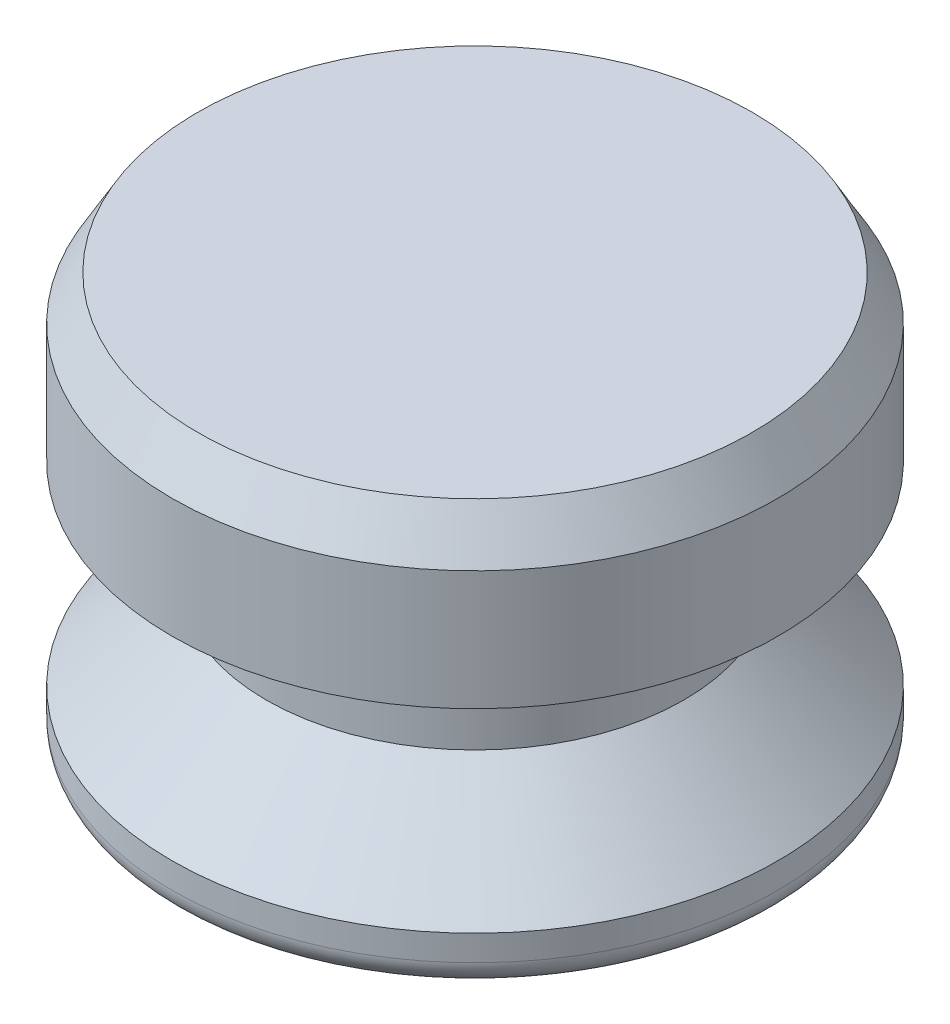
SolidWorks part; units mm, degrees
ref_plane "Front Plane" through (0, 0, 0) normal (0, 0, 1) x (1, 0, 0)
ref_plane "Top Plane" through (0, 0, 0) normal (0, 1, 0) x (1, 0, 0)
ref_plane "Right Plane" through (0, 0, 0) normal (1, 0, 0) x (0, 0, -1)
sketch "Sketch1" plane through (0, 0, 0) normal (0, 0, 1) x (1, 0, 0)
  line L0 (0, 0) -> (0, 12.7) construction
  line L1 (0, 0) -> (-9.398, 0)
  line L2 (-9.398, 0) -> (-9.398, 1.5875)
  line L4 (-6.477, 4.445) -> (-6.477, 7.62)
  line L5 (-6.477, 7.62) -> (-9.398, 7.62)
  line L6 (-9.398, 7.62) -> (-9.398, 12.7)
  line L7 (-9.398, 12.7) -> (0, 12.7)
  line L8 (-9.525, 16.6801) -> (-9.525, -9.6051) construction
  line L9 (0, 0) -> (0, 12.7)
  line L10 (-6.477, 4.445) -> (-9.398, 1.5875)
  dimension "D1" = 12.7
  dimension "D2" = 9.398
  dimension "D3" = 3.175
  dimension "D4" = 1.5875
  dimension "D5" = 9.525
  dimension "D6" = 6.477
  dimension "D7" = 7.62
revolve "Revolve1" add sketch "Sketch1" angle 360 about L9
fillet "Fillet1" radius 0.7937 1 edges at (0, 0, -9.398)
chamfer "Chamfer1" distance 0.7937 angle 60 1 edges at (0, 12.7, -9.398)
